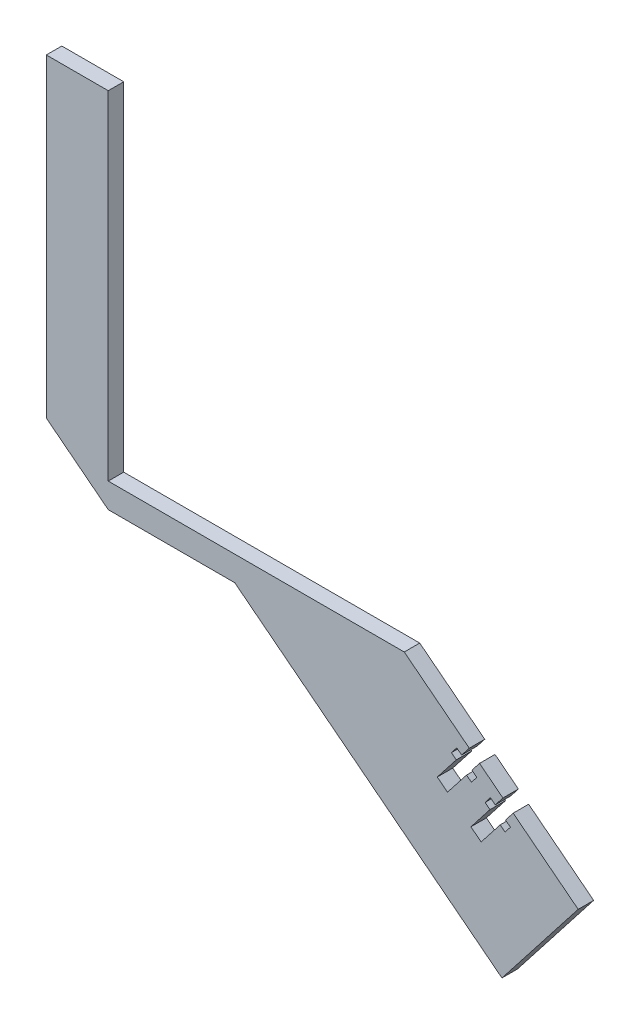
SolidWorks part; units mm, degrees
ref_plane "Front Plane" through (0, 0, 0) normal (0, 0, 1) x (1, 0, 0)
ref_plane "Top Plane" through (0, 0, 0) normal (0, 1, 0) x (1, 0, 0)
ref_plane "Right Plane" through (0, 0, 0) normal (1, 0, 0) x (0, 0, -1)
sketch "Sketch3" plane through (0, 0, -218) normal (0, 0, 1) x (1, 0, 0)
  line L0 (-331.8267, 452.4789) -> (-275.6472, 408.5867)
  line L1 (-447.4324, 585.7679) -> (-447.4324, 492.0393) construction
  line L2 (-275.6472, 408.5867) -> (-300.2737, 377.0662)
  line L3 (-300.2737, 377.0662) -> (-386.5579, 444.4789)
  line L4 (-335.6665, 455.4789) -> (-334.9846, 455.4789) construction
  line L5 (-275.6472, 408.5867) -> (-237.9324, 408.5867) construction
  line L6 (-331.8267, 452.4789) -> (-427.4324, 452.4789)
  line L7 (-237.9324, 312.3679) -> (-237.9324, 653.2679) construction
  line L10 (-427.4324, 561.68) -> (-447.4324, 561.68)
  line L11 (-427.4324, 452.4789) -> (-427.4324, 561.68)
  line L13 (-447.4324, 561.68) -> (-447.4324, 460.1046)
  line L15 (-386.5579, 444.4789) -> (-427.4324, 444.4789)
  line L16 (-427.4324, 444.4789) -> (-447.4324, 460.1046)
  line L18 (-329.0176, 450.2842) -> (-335.6665, 455.4789) construction
  line L19 (-447.4324, 492.0393) -> (-287.699, 367.2419) construction
  dimension "D1" = 8
  dimension "D2" = 3
  dimension "D3" = 20
extrude "Boss-Extrude1" add sketch "Sketch3" against normal blind 5
sketch "Sketch4" plane through (0, 0, -223) normal (0, 0, -1) x (-1, 0, 0)
  line L12 (296.6476, 424.994) -> (299.9573, 427.5798)
  line L13 (296.6476, 424.994) -> (299.1103, 421.8419)
  line L14 (299.9573, 427.5798) -> (302.4199, 424.4277)
  line L15 (297.5342, 420.6106) -> (299.1103, 421.8419)
  line L16 (297.5342, 420.6106) -> (299.2581, 418.4042)
  line L17 (303.9959, 425.659) -> (305.7198, 423.4526)
  line L18 (299.2581, 418.4042) -> (300.8341, 419.6355)
  line L19 (300.8341, 419.6355) -> (306.9907, 411.7554)
  line L20 (304.1438, 422.2213) -> (310.3004, 414.3412)
  line L21 (306.9907, 411.7554) -> (310.3004, 414.3412)
  line L22 (304.1438, 422.2213) -> (305.7198, 423.4526)
  line L23 (302.4199, 424.4277) -> (303.9959, 425.659)
  line L24 (308.6456, 413.0483) -> (296.4555, 428.6509) construction
  line L25 (275.6472, 408.5867) -> (331.8267, 452.4789) construction
  line L27 (275.6472, 408.5867) -> (331.8267, 452.4789) construction
  line L28 (291.021, 424.405) -> (301.89, 432.8968) construction
  line L29 (319.5145, 421.5401) -> (307.3245, 437.1427) construction
  line L30 (301.89, 432.8968) -> (316.9729, 413.5915) construction
  line L31 (309.9793, 430.3337) -> (308.4032, 429.1024)
  line L32 (311.7031, 428.1273) -> (310.1271, 426.896)
  line L33 (321.1694, 422.833) -> (317.8597, 420.2472)
  line L34 (311.7031, 428.1273) -> (317.8597, 420.2472)
  line L35 (315.0128, 430.7131) -> (321.1694, 422.833)
  line L36 (316.5888, 431.9444) -> (315.0128, 430.7131)
  line L37 (308.4032, 429.1024) -> (310.1271, 426.896)
  line L38 (314.8649, 434.1508) -> (316.5888, 431.9444)
  line L39 (314.8649, 434.1508) -> (313.2889, 432.9195)
  line L40 (307.5166, 433.4858) -> (309.9793, 430.3337)
  line L41 (310.8263, 436.0715) -> (313.2889, 432.9195)
  line L42 (310.8263, 436.0715) -> (307.5166, 433.4858)
  point P30 (303.7369, 430.5328)
  dimension "D1" = 4.2
  dimension "D2" = 2
  dimension "D3" = 2
  dimension "D4" = 2.8
  dimension "D5" = 10
  dimension "D6" = 4
extrude "Cut-Extrude1" cut sketch "Sketch4" against normal through all both and the other way through all
